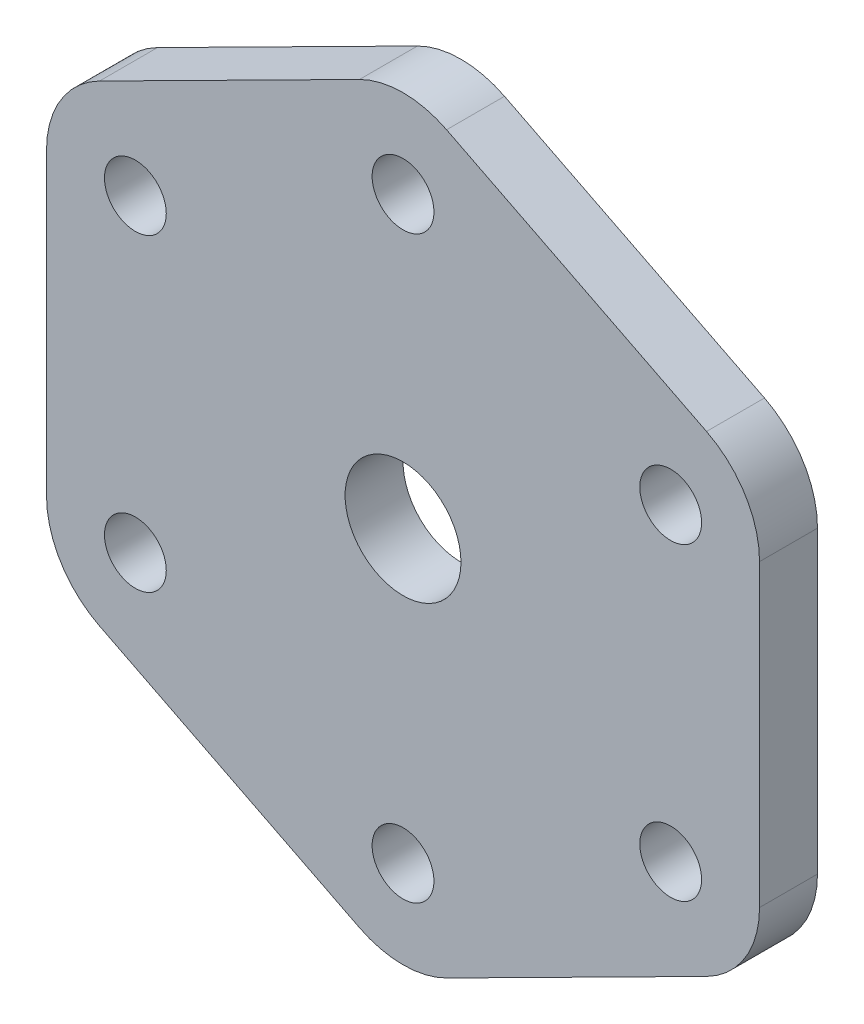
SolidWorks part; units mm, degrees
ref_plane "Plano frontal" through (0, 0, 0) normal (0, 0, 1) x (1, 0, 0)
ref_plane "Plano superior" through (0, 0, 0) normal (0, 1, 0) x (1, 0, 0)
ref_plane "Plano direito" through (0, 0, 0) normal (1, 0, 0) x (0, 0, -1)
ref_plane "Plano1" through (0, 0, -13) normal (0, 0, -1) x (-1, 0, 0)
sketch "Esboço1" plane through (0, 0, -13) normal (0, 0, -1) x (-1, 0, 0)
  line L0 (-18.4564, 7.7539) -> (-18.4564, -7.7539)
  line L1 (-15.711, -12.2168) -> (-2.2545, -19.0147)
  line L2 (2.2545, -19.0147) -> (15.711, -12.2168)
  line L3 (18.4564, -7.7539) -> (18.4564, 7.7539)
  line L4 (15.711, 12.2168) -> (2.2545, 19.0147)
  line L5 (-2.2545, 19.0147) -> (-15.711, 12.2168)
  line L6 (-13.8564, 8) -> (13.8564, -8) construction
  line L7 (0, -15) -> (0, 15) construction
  circle A0 centre (13.8564, -8) radius 1.6
  circle A1 centre (-13.8564, 8) radius 1.6
  circle A2 centre (13.8564, 8) radius 1.6
  circle A3 centre (0, 0) radius 3
  circle A4 centre (0, 15) radius 1.6
  circle A5 centre (-13.8564, -8) radius 1.6
  circle A6 centre (0, -15) radius 1.6
  arc A7 (-18.4564, -7.7539) -> (-15.711, -12.2168) centre (-13.4564, -7.7539) ccw
  arc A8 (-2.2545, -19.0147) -> (2.2545, -19.0147) centre (0, -14.5519) ccw
  arc A9 (15.711, -12.2168) -> (18.4564, -7.7539) centre (13.4564, -7.7539) ccw
  arc A10 (18.4564, 7.7539) -> (15.711, 12.2168) centre (13.4564, 7.7539) ccw
  arc A11 (2.2545, 19.0147) -> (-2.2545, 19.0147) centre (0, 14.5519) ccw
  arc A12 (-15.711, 12.2168) -> (-18.4564, 7.7539) centre (-13.4564, 7.7539) ccw
  point P32 (0, 0)
  dimension "D1" = 6
  dimension "D2" = 3.2
  dimension "D6" = 5
  dimension "D8" = 4.6
  dimension "D9" = 4.6
  dimension "D11" = 4.6
  dimension "D13" = 4.6
  dimension "D16" = 4.6
  dimension "D3" = 27.7128
  dimension "D4" = 16
  dimension "D5" = 30
  dimension "D7" = 4.6
  dimension "D10" = 4.6
  dimension "D12" = 4.6
  dimension "D14" = 4.6
  dimension "D15" = 4.6
extrude "Ressalto-extrusão1" add sketch "Esboço1" against normal blind 3
